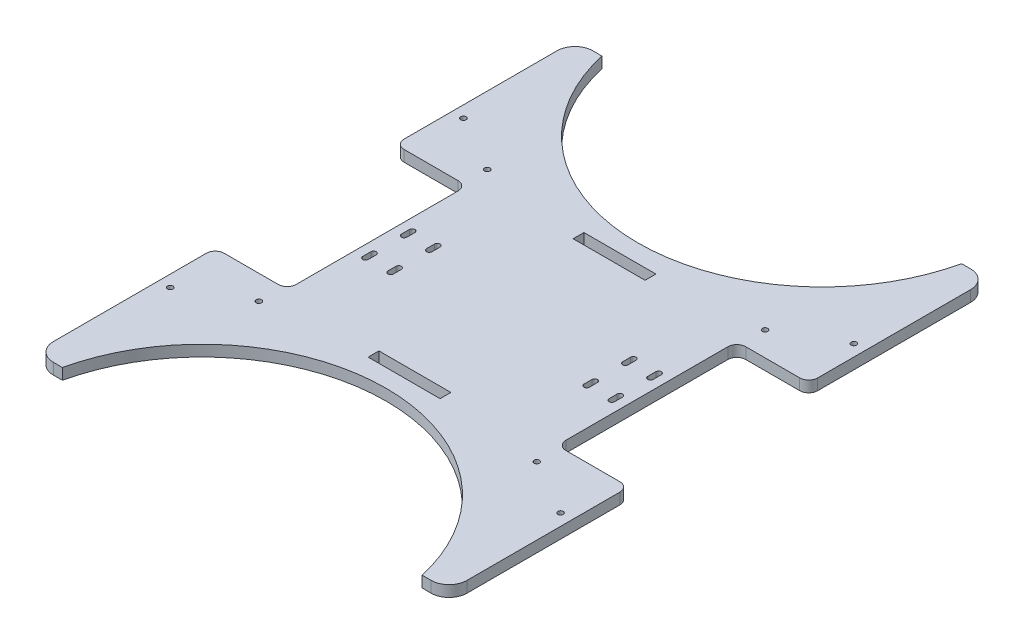
SolidWorks part; units mm, degrees
ref_plane "Front" through (0, 0, 0) normal (0, 0, 1) x (1, 0, 0)
ref_plane "Top" through (0, 0, 0) normal (0, 1, 0) x (1, 0, 0)
ref_plane "Right" through (0, 0, 0) normal (1, 0, 0) x (0, 0, -1)
sketch "草图1" plane through (0, 0, 0) normal (0, 1, 0) x (1, 0, 0)
  line L0 (18.586, 33.2218) -> (228.586, 33.2218)
  line L1 (238.586, 23.2218) -> (238.586, -256.7782)
  line L2 (228.586, -266.7782) -> (18.586, -266.7782)
  line L3 (8.586, -256.7782) -> (8.586, 23.2218)
  line L4 (8.586, 33.2218) -> (7.9071, 35.506)
  line L5 (-152.8763, -116.7782) -> (305.003, -116.7782) construction
  line L6 (88.586, 33.2218) -> (88.586, -300.1665) construction
  arc A0 (238.586, -256.7782) -> (228.586, -266.7782) centre (228.586, -256.7782) cw
  arc A1 (18.586, -266.7782) -> (8.586, -256.7782) centre (18.586, -256.7782) cw
  arc A2 (238.586, 23.2218) -> (228.586, 33.2218) centre (228.586, 23.2218) ccw
  arc A3 (18.586, 33.2218) -> (8.586, 23.2218) centre (18.586, 23.2218) ccw
  point P11 (238.586, -266.7782)
  point P16 (238.586, 33.2218)
  dimension "D3" = 10
  dimension "D1" = 230
  dimension "D2" = 300
extrude "凸台-拉伸1" add sketch "草图1" along normal blind 6.18 contours L0 A3 L3 A1 L2 A0 L1 A2
sketch "草图2" plane through (0, 6.18, 0) normal (0, 1, 0) x (1, 0, 0)
  line L0 (48.586, -161.7782) -> (48.586, -71.7782)
  line L1 (8.586, -256.7782) -> (8.586, 23.2218) construction
  line L2 (123.586, 33.2218) -> (123.586, -266.7782) construction
  line L3 (43.586, -66.7782) -> (8.586, -66.7782)
  line L4 (8.586, -66.7782) -> (8.586, -166.7782)
  line L5 (8.586, -166.7782) -> (43.586, -166.7782)
  line L6 (55.086, -103.7782) -> (55.086, -108.2782) construction
  line L7 (18.586, 33.2218) -> (228.586, 33.2218) construction
  line L8 (228.586, -266.7782) -> (18.586, -266.7782) construction
  line L9 (56.586, -103.7782) -> (56.586, -108.2782)
  line L10 (53.586, -103.7782) -> (53.586, -108.2782)
  line L11 (-61.414, -116.7782) -> (61.414, -116.7782) construction
  line L12 (69.086, -103.7782) -> (69.086, -108.2782) construction
  line L13 (70.586, -103.7782) -> (70.586, -108.2782)
  line L14 (67.586, -103.7782) -> (67.586, -108.2782)
  line L15 (69.086, -129.7782) -> (69.086, -125.2782) construction
  line L16 (70.586, -129.7782) -> (70.586, -125.2782)
  line L17 (67.586, -129.7782) -> (67.586, -125.2782)
  line L18 (55.086, -129.7782) -> (55.086, -125.2782) construction
  line L19 (56.586, -129.7782) -> (56.586, -125.2782)
  line L20 (53.586, -129.7782) -> (53.586, -125.2782)
  line L21 (178.086, -129.7782) -> (178.086, -125.2782) construction
  line L22 (176.586, -129.7782) -> (176.586, -125.2782)
  line L23 (179.586, -129.7782) -> (179.586, -125.2782)
  line L24 (192.086, -129.7782) -> (192.086, -125.2782) construction
  line L25 (190.586, -129.7782) -> (190.586, -125.2782)
  line L26 (193.586, -129.7782) -> (193.586, -125.2782)
  line L27 (192.086, -103.7782) -> (192.086, -108.2782) construction
  line L28 (190.586, -103.7782) -> (190.586, -108.2782)
  line L29 (193.586, -103.7782) -> (193.586, -108.2782)
  line L30 (178.086, -103.7782) -> (178.086, -108.2782) construction
  line L31 (176.586, -103.7782) -> (176.586, -108.2782)
  line L32 (179.586, -103.7782) -> (179.586, -108.2782)
  line L34 (198.586, -161.7782) -> (198.586, -71.7782)
  line L35 (238.586, -66.7782) -> (238.586, -166.7782)
  line L36 (203.586, -66.7782) -> (238.586, -66.7782)
  line L37 (238.586, -166.7782) -> (203.586, -166.7782)
  arc A0 (56.586, -103.7782) -> (53.586, -103.7782) centre (55.086, -103.7782) ccw
  arc A1 (53.586, -108.2782) -> (56.586, -108.2782) centre (55.086, -108.2782) ccw
  arc A2 (70.586, -103.7782) -> (67.586, -103.7782) centre (69.086, -103.7782) ccw
  arc A3 (67.586, -108.2782) -> (70.586, -108.2782) centre (69.086, -108.2782) ccw
  arc A4 (70.586, -129.7782) -> (67.586, -129.7782) centre (69.086, -129.7782) cw
  arc A5 (67.586, -125.2782) -> (70.586, -125.2782) centre (69.086, -125.2782) cw
  arc A6 (56.586, -129.7782) -> (53.586, -129.7782) centre (55.086, -129.7782) cw
  arc A7 (53.586, -125.2782) -> (56.586, -125.2782) centre (55.086, -125.2782) cw
  arc A8 (176.586, -129.7782) -> (179.586, -129.7782) centre (178.086, -129.7782) ccw
  arc A9 (179.586, -125.2782) -> (176.586, -125.2782) centre (178.086, -125.2782) ccw
  arc A10 (190.586, -129.7782) -> (193.586, -129.7782) centre (192.086, -129.7782) ccw
  arc A11 (193.586, -125.2782) -> (190.586, -125.2782) centre (192.086, -125.2782) ccw
  arc A12 (190.586, -103.7782) -> (193.586, -103.7782) centre (192.086, -103.7782) cw
  arc A13 (193.586, -108.2782) -> (190.586, -108.2782) centre (192.086, -108.2782) cw
  arc A14 (176.586, -103.7782) -> (179.586, -103.7782) centre (178.086, -103.7782) cw
  arc A15 (179.586, -108.2782) -> (176.586, -108.2782) centre (178.086, -108.2782) cw
  arc A16 (43.586, -166.7782) -> (48.586, -161.7782) centre (43.586, -161.7782) ccw
  arc A17 (48.586, -71.7782) -> (43.586, -66.7782) centre (43.586, -71.7782) ccw
  arc A18 (203.586, -166.7782) -> (198.586, -161.7782) centre (203.586, -161.7782) cw
  arc A19 (198.586, -71.7782) -> (203.586, -66.7782) centre (203.586, -71.7782) cw
  point P16 (55.086, -106.0282)
  point P21 (69.086, -106.0282)
  point P28 (0, -116.7782)
  point P29 (55.086, -102.2782)
  point P30 (69.086, -102.2782)
  point P33 (69.086, -127.5282)
  point P40 (55.086, -127.5282)
  point P47 (178.086, -127.5282)
  point P54 (192.086, -127.5282)
  point P61 (192.086, -106.0282)
  point P68 (178.086, -106.0282)
  point P76 (48.586, -166.7782)
  point P79 (48.586, -66.7782)
  point P82 (198.586, -166.7782)
  point P85 (198.586, -66.7782)
  dimension "D5" = 40
  dimension "D7" = 1.5
  dimension "D9" = 5
  dimension "D11" = 17
  dimension "D14" = 5
  dimension "D6" = 1.5
  dimension "D2" = 4.5
  dimension "D3" = 100
  dimension "D4" = 4.5
  dimension "D8" = 14.5
  dimension "D10" = 14.5
  dimension "D12" = 5
extrude "切除-拉伸1" cut sketch "草图2" against normal through all
fillet "圆角2" radius 5 1 edges at (8.586, 3.09, 66.7782)
fillet "圆角3" radius 5 1 edges at (8.586, 3.09, 166.7782)
fillet "圆角4" radius 5 1 edges at (238.586, 3.09, 166.7782)
fillet "圆角5" radius 5 1 edges at (238.586, 3.09, 66.7782)
sketch "草图4" plane through (0, 0, 0) normal (0, -1, 0) x (-1, 0, 0)
  line L0 (-123.586, -59.7782) -> (-123.586, -56.7782)
  line L1 (-123.586, -59.7782) -> (-123.586, -62.7782)
  line L2 (-8.586, -61.7782) -> (-8.586, 23.2218) construction
  line L3 (-123.586, -62.7782) -> (-143.586, -62.7782)
  line L4 (-143.586, -62.7782) -> (-143.586, -56.7782)
  line L5 (-143.586, -56.7782) -> (-103.586, -56.7782)
  line L6 (-103.586, -56.7782) -> (-103.586, -62.7782)
  line L7 (-103.586, -62.7782) -> (-123.586, -62.7782)
  line L8 (-123.586, -170.7782) -> (-143.586, -170.7782)
  line L9 (-143.586, -170.7782) -> (-143.586, -176.7782)
  line L10 (-143.586, -176.7782) -> (-103.586, -176.7782)
  line L11 (-103.586, -170.7782) -> (-123.586, -170.7782)
  line L12 (-103.586, -176.7782) -> (-103.586, -170.7782)
  line L13 (-43.586, -66.7782) -> (-13.586, -66.7782) construction
  line L20 (-198.586, -116.7782) -> (-48.586, -116.7782) construction
  line L21 (-198.586, -71.7782) -> (-198.586, -161.7782) construction
  line L22 (-48.586, -161.7782) -> (-48.586, -71.7782) construction
  line L23 (-123.586, 33.2218) -> (-123.586, -266.7782) construction
  line L24 (-18.586, 33.2218) -> (-228.586, 33.2218) construction
  line L25 (-228.586, -266.7782) -> (-18.586, -266.7782) construction
  circle A0 centre (-232.1139, -35.2497) radius 1.5
  circle A1 centre (-200.8381, -53.3068) radius 1.5
  circle A2 centre (-232.1139, -198.3068) radius 1.5
  circle A3 centre (-200.8381, -180.2497) radius 1.5
  circle A4 centre (-15.0581, -198.3068) radius 1.5
  circle A5 centre (-46.3339, -180.2497) radius 1.5
  circle A6 centre (-46.3339, -53.3068) radius 1.5
  circle A7 centre (-15.0581, -35.2497) radius 1.5
  point P42 (0, 0)
  dimension "D6" = 6.4721
  dimension "D2" = 3
  dimension "D4" = 3
  dimension "D1" = 10
  dimension "D3" = 3
  dimension "D8" = 40
  dimension "D9" = 6
extrude "切除-拉伸2" cut sketch "草图4" against normal through all
sketch "草图5" plane through (0, 6.18, 0) normal (0, 1, 0) x (1, 0, 0)
  line L1 (123.586, -266.7782) -> (23.586, -266.7782)
  line L2 (48.586, -116.7782) -> (198.586, -116.7782) construction
  line L3 (228.586, -266.7782) -> (18.586, -266.7782) construction
  line L4 (123.586, -266.7782) -> (223.586, -266.7782)
  line L5 (48.586, -161.7782) -> (48.586, -71.7782) construction
  line L6 (143.586, -176.7782) -> (103.586, -176.7782) construction
  line L7 (198.586, -71.7782) -> (198.586, -161.7782) construction
  line L8 (23.586, 33.2218) -> (223.586, 33.2218)
  arc A0 (23.586, -266.7782) -> (223.586, -266.7782) centre (123.586, -289.2782) cw
  arc A1 (23.586, 33.2218) -> (223.586, 33.2218) centre (123.586, 55.7218) ccw
  point P5 (123.586, -186.7782)
  point P27 (123.586, -176.7782)
  dimension "D1" = 100
  dimension "D2" = 100
  dimension "D3" = 10
extrude "切除-拉伸9" cut sketch "草图5" against normal through all and the other way through all
